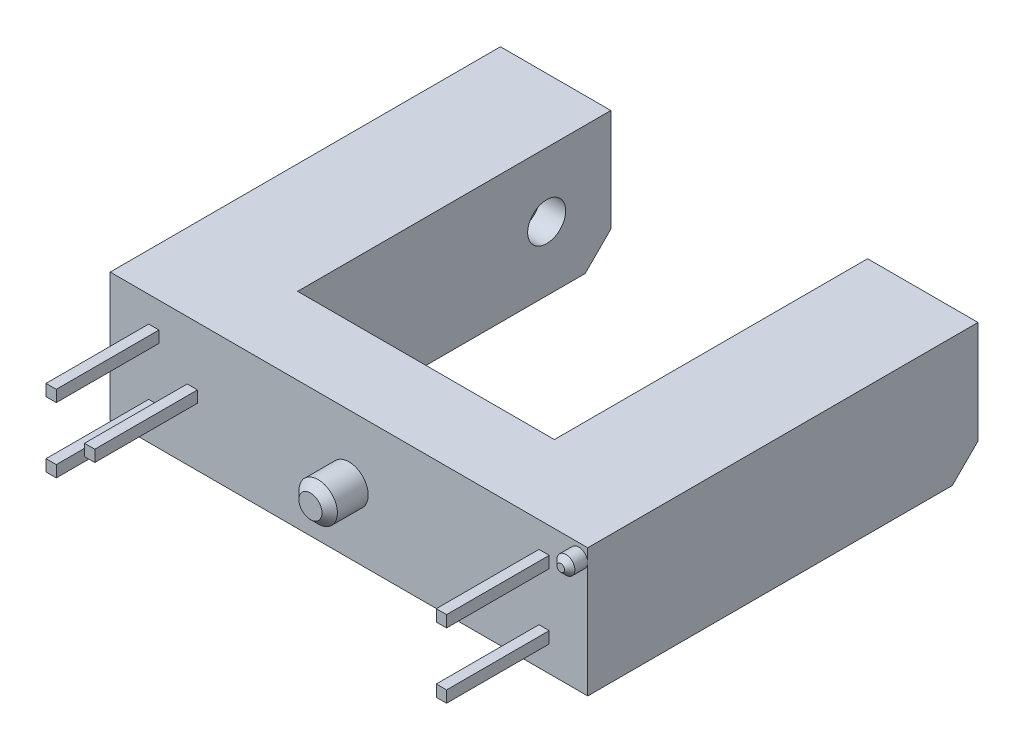
SolidWorks part; units mm, degrees
ref_plane "Front Plane" through (0, 0, 0) normal (0, 0, 1) x (1, 0, 0)
ref_plane "Top Plane" through (0, 0, 0) normal (0, 1, 0) x (1, 0, 0)
ref_plane "Right Plane" through (0, 0, 0) normal (1, 0, 0) x (0, 0, -1)
sketch "Sketch1" plane through (0, 0, 0) normal (0, 1, 0) x (1, 0, 0)
  line L0 (5, 2.5) -> (9.3, 2.5)
  line L1 (-9.3, 2.5) -> (-5, 2.5)
  line L2 (-9.3, 2.5) -> (-9.3, -12.7)
  line L3 (-9.3, -12.7) -> (9.3, -12.7)
  line L4 (9.3, 2.5) -> (9.3, -12.7)
  line L5 (-5, 0) -> (5, 0) construction
  line L6 (5, 2.5) -> (5, -9.7)
  line L7 (5, -9.7) -> (-5, -9.7)
  line L8 (-5, 2.5) -> (-5, -9.7)
  dimension "D1" = 10
  dimension "D2" = 18.6
  dimension "D3" = 2.5
  dimension "D4" = 15.2
  dimension "D5" = 3
extrude "Boss-Extrude1" add sketch "Sketch1" along normal mid plane 5
sketch "Sketch3" plane through (0, 0, 12.7) normal (0, 0, 1) x (1, 0, 0)
  circle A0 centre (0, 0) radius 0.75
  dimension "D1" = 1.5
extrude "Boss-Extrude2" add sketch "Sketch3" along normal blind 1.5
sketch "Sketch4" plane through (0, 0, 12.7) normal (0, 0, 1) x (1, 0, 0)
  circle A0 centre (8.95, 2) radius 0.35
  dimension "D3" = 0.7
  dimension "D1" = 2
  dimension "D2" = 8.95
extrude "Boss-Extrude3" add sketch "Sketch4" along normal blind 0.7
chamfer "Chamfer1" distance 0.2 angle 45 1 edges at (9.3, 2, 13.4)
chamfer "Chamfer2" distance 0.3 angle 45 1 edges at (0.75, 0, 14.2)
chamfer "Chamfer3" distance 1 angle 45 2 edges at (-7.15, -2.5, -2.5) (7.15, -2.5, -2.5)
sketch "Sketch5" plane through (0, 0, 12.7) normal (0, 0, 1) x (1, 0, 0)
  line L0 (7.8, -1.27) -> (-7.8, -1.27) construction
  line L1 (-7.8, 1.495) -> (-7.4, 1.495)
  line L2 (-7.8, 1.495) -> (-7.8, 1.045)
  line L3 (-7.8, 1.045) -> (-7.4, 1.045)
  line L4 (-7.4, 1.495) -> (-7.4, 1.045)
  line L5 (-7.8, -1.045) -> (-7.4, -1.045)
  line L6 (-7.8, -1.045) -> (-7.8, -1.495)
  line L7 (-7.8, -1.495) -> (-7.4, -1.495)
  line L8 (-7.4, -1.045) -> (-7.4, -1.495)
  line L9 (-6.3, 0.225) -> (-5.9, 0.225)
  line L10 (-6.3, 0.225) -> (-6.3, -0.225)
  line L11 (-6.3, -0.225) -> (-5.9, -0.225)
  line L12 (-5.9, 0.225) -> (-5.9, -0.225)
  line L13 (7.4, 1.495) -> (7.8, 1.495)
  line L14 (7.4, 1.495) -> (7.4, 1.045)
  line L15 (7.4, 1.045) -> (7.8, 1.045)
  line L16 (7.8, 1.495) -> (7.8, 1.045)
  line L17 (7.4, -1.045) -> (7.8, -1.045)
  line L18 (7.4, -1.045) -> (7.4, -1.495)
  line L19 (7.4, -1.495) -> (7.8, -1.495)
  line L20 (7.8, -1.045) -> (7.8, -1.495)
  line L21 (-7.8, 1.27) -> (7.8, 1.27) construction
  line L22 (0, 1.27) -> (0, -1.27) construction
  line L23 (0, 0) -> (-5.9, 0) construction
  dimension "D1" = 0.45
  dimension "D2" = 0.4
  dimension "D3" = 1.5
  dimension "D4" = 2.54
  dimension "D5" = 15.2
extrude "Boss-Extrude4" add sketch "Sketch5" along normal blind 4
sketch "Sketch6" plane through (-5, 0, 0) normal (1, 0, 0) x (0, 0, -1)
  circle A0 centre (0, 0) radius 0.7403
extrude "Cut-Extrude1" cut sketch "Sketch6" against normal blind 1
